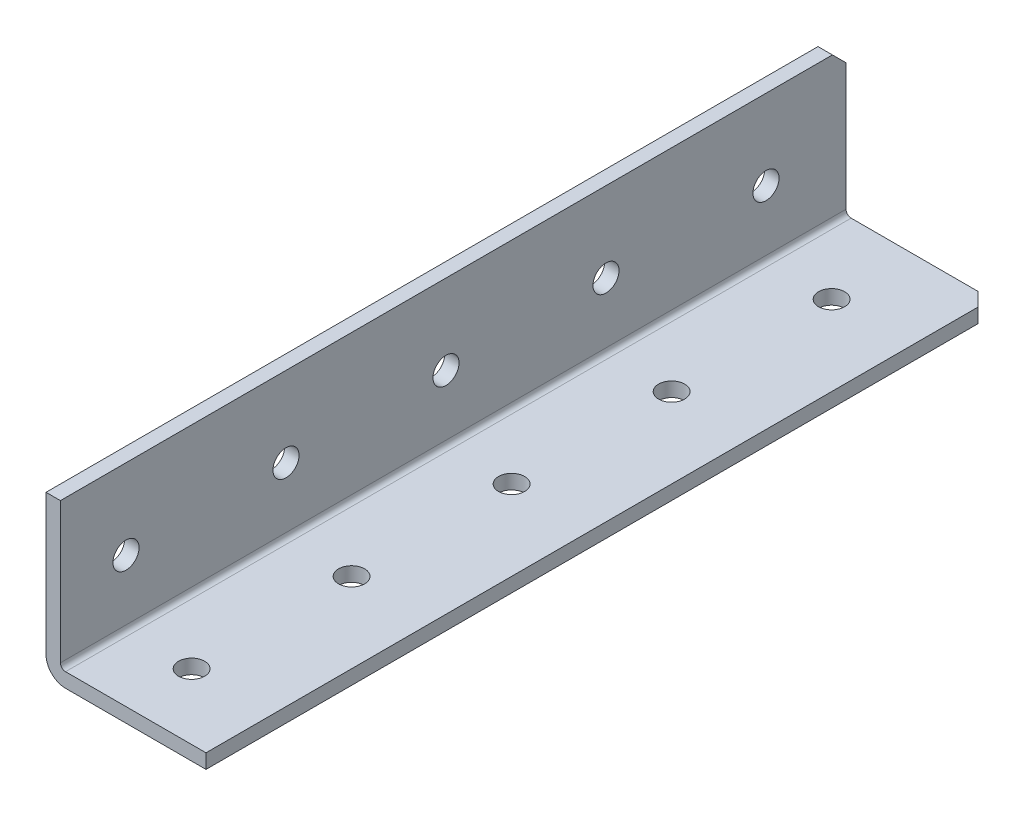
SolidWorks part; units mm, degrees
material "6061-T6 (SS)"
ref_plane "Front Plane" through (0, 0, 0) normal (0, 0, 1) x (1, 0, 0)
ref_plane "Top Plane" through (0, 0, 0) normal (0, 1, 0) x (1, 0, 0)
ref_plane "Right Plane" through (0, 0, 0) normal (1, 0, 0) x (0, 0, -1)
ref_plane "Plane1" through (0, 0, 0) normal (-1, 0, 0) x (0, -1, 0)
sketch "Sketch1" plane through (0, 0, 0) normal (-1, 0, 0) x (0, -1, 0)
  line L0 (0, 749.3) -> (-25.4, 749.3)
  line L1 (-25.4, 749.3) -> (-25.4, -749.3)
  line L2 (-25.4, -749.3) -> (0, -749.3)
  line L3 (0, -749.3) -> (0, 749.3)
extrude "Boss-Extrude1" add sketch "Sketch1" against normal blind 25.4
sketch "Sketch2" plane through (0, 0, -749.3) normal (0, 0, -1) x (-1, 0, 0)
  line L0 (-25.4, 2.286) -> (-2.286, 2.286)
  line L1 (-2.286, 2.286) -> (-2.286, 25.4)
  line L2 (-2.286, 25.4) -> (-25.4, 25.4)
  line L3 (-25.4, 25.4) -> (-25.4, 2.286)
extrude "Cut-Extrude1" cut sketch "Sketch2" against normal through all
hole_wizard "M3.5 Clearance Hole1" positions "Sketch4" profile "Sketch3" hole size "M3.5" standard "ANSI Metric"
sketch "Sketch4" plane through (0, 0, 0) normal (0, -1, 0) x (-1, 0, 0)
  point P0 (-12.7, 736.6)
  point P1 (-12.7, 711.2)
  point P2 (-12.7, 685.8)
  point P3 (-12.7, 660.4)
  point P4 (-12.7, 635)
  point P5 (-12.7, 609.6)
  point P6 (-12.7, 584.2)
  point P7 (-12.7, 558.8)
  point P8 (-12.7, 533.4)
  point P9 (-12.7, 508)
  point P10 (-12.7, 482.6)
  point P11 (-12.7, 457.2)
  point P12 (-12.7, 431.8)
  point P13 (-12.7, 406.4)
  point P14 (-12.7, 381)
  point P15 (-12.7, 355.6)
  point P16 (-12.7, 330.2)
  point P17 (-12.7, 304.8)
  point P18 (-12.7, 279.4)
  point P19 (-12.7, 254)
  point P20 (-12.7, 228.6)
  point P21 (-12.7, 203.2)
  point P22 (-12.7, 177.8)
  point P23 (-12.7, 152.4)
  point P24 (-12.7, 127)
  point P25 (-12.7, 101.6)
  point P26 (-12.7, 76.2)
  point P27 (-12.7, 50.8)
  point P28 (-12.7, 25.4)
  point P29 (-12.7, 0)
  point P30 (-12.7, -25.4)
  point P31 (-12.7, -50.8)
  point P32 (-12.7, -76.2)
  point P33 (-12.7, -101.6)
  point P34 (-12.7, -127)
  point P35 (-12.7, -152.4)
  point P36 (-12.7, -177.8)
  point P37 (-12.7, -203.2)
  point P38 (-12.7, -228.6)
  point P39 (-12.7, -254)
  point P40 (-12.7, -279.4)
  point P41 (-12.7, -304.8)
  point P42 (-12.7, -330.2)
  point P43 (-12.7, -355.6)
  point P44 (-12.7, -381)
  point P45 (-12.7, -406.4)
  point P46 (-12.7, -431.8)
  point P47 (-12.7, -457.2)
  point P48 (-12.7, -482.6)
  point P49 (-12.7, -508)
  point P50 (-12.7, -533.4)
  point P51 (-12.7, -558.8)
  point P52 (-12.7, -584.2)
  point P53 (-12.7, -609.6)
  point P54 (-12.7, -635)
  point P55 (-12.7, -660.4)
  point P56 (-12.7, -685.8)
  point P57 (-12.7, -711.2)
  point P58 (-12.7, -736.6)
sketch "Sketch3" plane through (12.7, 0, -736.6) normal (1, 0, 0) x (0, 0, -1)
  line L0 (0, 0) -> (0, 25.4)
  line L1 (0, 25.4) -> (2.0701, 25.4)
  line L2 (2.0701, 25.4) -> (2.0701, 0)
  line L5 (2.0701, 0) -> (0, 0)
  line L11 (0, -6.35) -> (0, 107.95) construction
  dimension "Thru Hole Dia." = 4.1402
  dimension "Thru Hole Depth" = 25.4
hole_wizard "M3.5 Clearance Hole2" positions "Sketch6" profile "Sketch5" hole size "M3.5" standard "ANSI Metric"
sketch "Sketch6" plane through (0, 0, 0) normal (-1, 0, 0) x (0, 0, 1)
  point P0 (711.2, 12.7)
  point P1 (736.6, 12.7)
  point P2 (685.8, 12.7)
  point P3 (660.4, 12.7)
  point P4 (635, 12.7)
  point P5 (609.6, 12.7)
  point P6 (584.2, 12.7)
  point P7 (558.8, 12.7)
  point P8 (533.4, 12.7)
  point P9 (508, 12.7)
  point P10 (482.6, 12.7)
  point P11 (457.2, 12.7)
  point P12 (431.8, 12.7)
  point P13 (406.4, 12.7)
  point P14 (381, 12.7)
  point P15 (355.6, 12.7)
  point P16 (330.2, 12.7)
  point P17 (304.8, 12.7)
  point P18 (279.4, 12.7)
  point P19 (254, 12.7)
  point P20 (228.6, 12.7)
  point P21 (203.2, 12.7)
  point P22 (177.8, 12.7)
  point P23 (152.4, 12.7)
  point P24 (127, 12.7)
  point P25 (101.6, 12.7)
  point P26 (76.2, 12.7)
  point P27 (50.8, 12.7)
  point P28 (25.4, 12.7)
  point P29 (0, 12.7)
  point P30 (-25.4, 12.7)
  point P31 (-50.8, 12.7)
  point P32 (-76.2, 12.7)
  point P33 (-101.6, 12.7)
  point P34 (-127, 12.7)
  point P35 (-152.4, 12.7)
  point P36 (-177.8, 12.7)
  point P37 (-203.2, 12.7)
  point P38 (-228.6, 12.7)
  point P39 (-254, 12.7)
  point P40 (-279.4, 12.7)
  point P41 (-304.8, 12.7)
  point P42 (-330.2, 12.7)
  point P43 (-355.6, 12.7)
  point P44 (-381, 12.7)
  point P45 (-406.4, 12.7)
  point P46 (-431.8, 12.7)
  point P47 (-457.2, 12.7)
  point P48 (-482.6, 12.7)
  point P49 (-508, 12.7)
  point P50 (-533.4, 12.7)
  point P51 (-558.8, 12.7)
  point P52 (-584.2, 12.7)
  point P53 (-609.6, 12.7)
  point P54 (-635, 12.7)
  point P55 (-660.4, 12.7)
  point P56 (-685.8, 12.7)
  point P57 (-711.2, 12.7)
  point P58 (-736.6, 12.7)
sketch "Sketch5" plane through (0, 12.7, 711.2) normal (0, 1, 0) x (0, 0, 1)
  line L0 (0, 0) -> (0, 25.4)
  line L1 (0, 25.4) -> (2.0701, 25.4)
  line L2 (2.0701, 25.4) -> (2.0701, 0)
  line L5 (2.0701, 0) -> (0, 0)
  line L11 (0, -6.35) -> (0, 107.95) construction
  dimension "Thru Hole Dia." = 4.1402
  dimension "Thru Hole Depth" = 25.4
chamfer "Chamfer1" distance 2.159 angle 45 4 edges at (25.4, 1.143, -749.3) (1.143, 25.4, -749.3) (1.143, 25.4, 749.3) (25.4, 1.143, 749.3)
fillet "Fillet1" radius 0.8128 1 edges at (2.286, 2.286, 0)
fillet "Fillet2" radius 3.0988 1 edges at (0, 0, 0)
sketch "Sketch8" plane through (0, 0, 749.3) normal (0, 0, 1) x (1, 0, 0)
  line L1 (-45.6555, -36.5704) -> (50.2275, -36.5704)
  line L2 (-45.6555, -36.5704) -> (-45.6555, 42.768)
  line L3 (-45.6555, 42.768) -> (50.2275, 42.768)
  line L4 (50.2275, -36.5704) -> (50.2275, 42.768)
  line L5 (-45.6555, -36.5704) -> (50.2275, 42.768) construction
  line L6 (-45.6555, 42.768) -> (50.2275, -36.5704) construction
  point P0 (2.286, 3.0988)
extrude "Cut-Extrude3" cut sketch "Sketch8" against normal blind 1371.6
sketch "Sketch11" plane through (0, 0, -622.3) normal (0, 0, 1) x (1, 0, 0)
  line L1 (-23.8761, -31.5895) -> (27.5864, -31.5895)
  line L2 (-23.8761, -31.5895) -> (-23.8761, 35.0872)
  line L3 (-23.8761, 35.0872) -> (27.5864, 35.0872)
  line L4 (27.5864, -31.5895) -> (27.5864, 35.0872)
  line L5 (-23.8761, -31.5895) -> (27.5864, 35.0872) construction
  line L6 (-23.8761, 35.0872) -> (27.5864, -31.5895) construction
  point P0 (1.8552, 1.7488)
extrude "Cut-Extrude6" cut sketch "Sketch11" against normal blind 2.286
